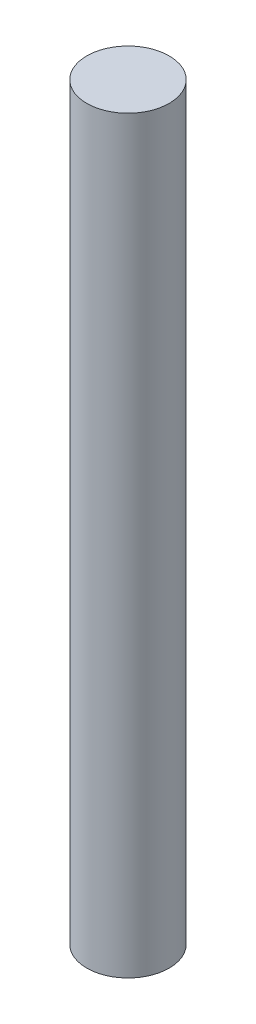
SolidWorks part; units mm, degrees
ref_plane "Front Plane" through (0, 0, 0) normal (0, 0, 1) x (1, 0, 0)
ref_plane "Top Plane" through (0, 0, 0) normal (0, 1, 0) x (1, 0, 0)
ref_plane "Right Plane" through (0, 0, 0) normal (1, 0, 0) x (0, 0, -1)
sketch "Sketch1" plane through (0, 0, 0) normal (0, 1, 0) x (1, 0, 0)
  circle A0 centre (0, 0) radius 2.75
  point P3 (-203.0085, 53.5402)
extrude "Boss-Extrude3" add sketch "Sketch1" along normal blind 50
